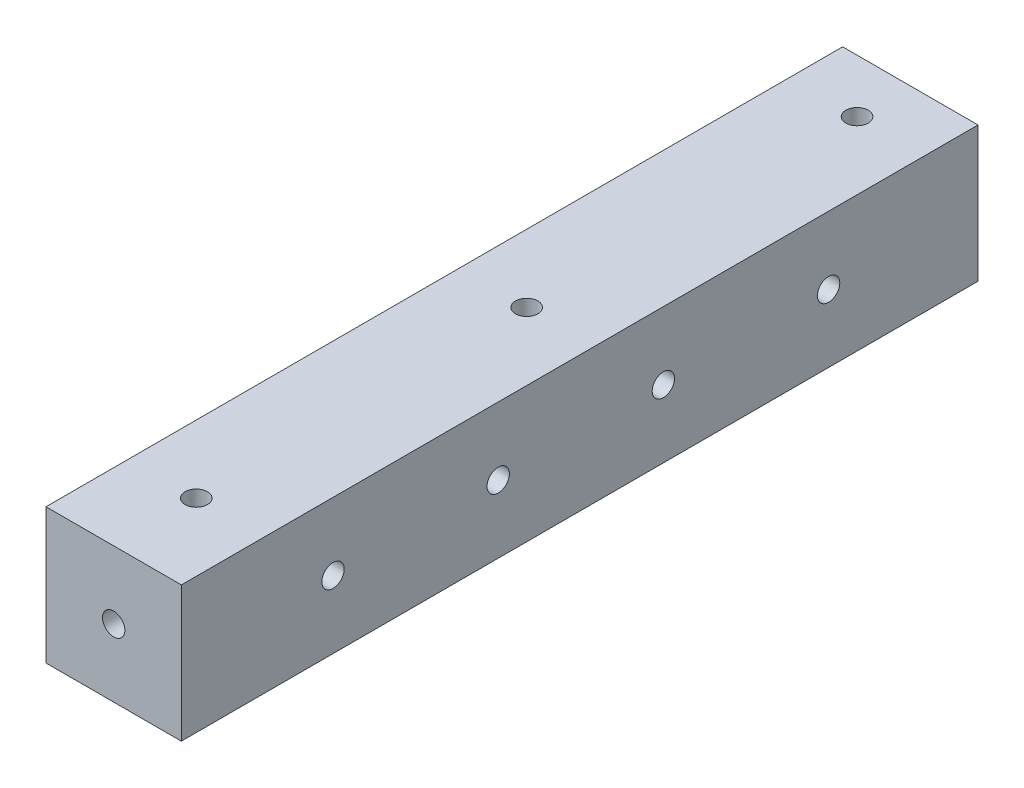
SolidWorks part; units mm, degrees
material "6061 Alloy"
ref_plane "Front Plane" through (0, 0, 0) normal (0, 0, 1) x (1, 0, 0)
ref_plane "Top Plane" through (0, 0, 0) normal (0, 1, 0) x (1, 0, 0)
ref_plane "Right Plane" through (0, 0, 0) normal (1, 0, 0) x (0, 0, -1)
sketch "Sketch1" plane through (0, 0, 0) normal (0, 0, 1) x (1, 0, 0)
  line L1 (-12.7, -12.7) -> (12.7, -12.7)
  line L2 (-12.7, -12.7) -> (-12.7, 12.7)
  line L3 (-12.7, 12.7) -> (12.7, 12.7)
  line L4 (12.7, -12.7) -> (12.7, 12.7)
  line L5 (-12.7, -12.7) -> (12.7, 12.7) construction
  line L6 (-12.7, 12.7) -> (12.7, -12.7) construction
  point P0 (0, 0)
  dimension "D1" = 25.4
extrude "Boss-Extrude1" add sketch "Sketch1" along normal mid plane 155
sketch "Sketch2" plane through (0, 0, 77.5) normal (0, 0, 1) x (1, 0, 0)
  point P0 (0, 0)
sketch "Sketch4" plane through (12.7, 0, 0) normal (1, 0, 0) x (0, 0, -1)
  line L0 (-77.5, -12.7) -> (-77.5, 12.7) construction
  point P0 (-46.5, 0)
  point P1 (-15.5, 0)
  point P2 (15.5, 0)
  point P3 (46.5, 0)
  dimension "D1" = 31
  dimension "D2" = 31
  dimension "D3" = 31
  dimension "D4" = 31
sketch "Sketch5" plane through (0, -12.7, 0) normal (0, -1, 0) x (1, 0, 0)
  line L0 (-12.7, 77.5) -> (12.7, 77.5) construction
  line L1 (-12.7, -77.5) -> (12.7, -77.5) construction
  point P0 (0, 62)
  point P1 (0, 0)
  point P2 (0, -62)
  dimension "D1" = 15.5
  dimension "D2" = 15.5
hole_wizard "M5x0.8 Tapped Hole3" positions "Sketch6" profile "Sketch8" tap size "M5x0.8" standard "ANSI Metric"
sketch "Sketch6" plane through (12.7, 0, 0) normal (1, 0, 0) x (0, 0, -1)
  point P0 (-46.5, 0)
  point P3 (-15.5, 0)
  point P6 (15.5, 0)
  point P9 (46.5, 0)
sketch "Sketch8" plane through (12.7, 0, 46.5) normal (0, 1, 0) x (0, 0, -1)
  line L0 (0, 0) -> (0, 25.4)
  line L1 (0, 25.4) -> (2.1, 25.4)
  line L2 (2.1, 25.4) -> (2.1, 0)
  line L5 (2.1, 0) -> (0, 0)
  line L11 (0, -6.35) -> (0, 107.95) construction
  dimension "Thru Tap Drill Dia." = 4.2
  dimension "Thru Tap Drill Depth" = 25.4
hole_wizard "M5x0.8 Tapped Hole2" positions "Sketch9" profile "Sketch10" tap size "M5x0.8" standard "ANSI Metric" end condition through all
sketch "Sketch9" plane through (0, -12.7, 0) normal (0, -1, 0) x (-1, 0, 0)
  point P0 (0, -62)
  point P3 (0, 0)
  point P6 (0, 62)
sketch "Sketch10" plane through (0, -12.7, 62) normal (1, 0, 0) x (0, 0, -1)
  line L0 (0, 0) -> (0, 25.4)
  line L1 (0, 25.4) -> (2.1, 25.4)
  line L2 (2.1, 25.4) -> (2.1, 0)
  line L5 (2.1, 0) -> (0, 0)
  line L11 (0, -6.35) -> (0, 107.95) construction
  dimension "Thru Tap Drill Dia." = 4.2
  dimension "Thru Tap Drill Depth" = 25.4
hole_wizard "M5x0.8 Tapped Hole1" positions "Sketch11" profile "Sketch12" tap size "M5x0.8" standard "ANSI Metric"
sketch "Sketch11" plane through (0, 0, 77.5) normal (0, 0, 1) x (1, 0, 0)
  point P0 (0, 0)
sketch "Sketch12" plane through (0, 0, 77.5) normal (1, 0, 0) x (0, -1, 0)
  line L0 (0, 0) -> (0, 11.2618)
  line L1 (0, 11.2618) -> (2.1, 10)
  line L2 (2.1, 10) -> (2.1, 0)
  line L5 (2.1, 0) -> (0, 0)
  line L10 (0, 11.2618) -> (-2.1, 10) construction
  line L11 (0, -6.35) -> (0, 107.95) construction
  dimension "Tap Drill Dia." = 4.2
  dimension "Tap Drill Depth" = 10
  dimension "Drill Angle" = 118
sketch "Sketch13" plane through (0, 12.7, 0) normal (0, 1, 0) x (1, 0, 0)
  line L0 (12.7, -77.5) -> (12.7, 77.5) construction
  line L1 (12.7, 72) -> (-12.7, 72)
  line L2 (12.7, 72) -> (12.7, 77.5)
  line L3 (12.7, 77.5) -> (-12.7, 77.5)
  line L4 (-12.7, 72) -> (-12.7, 77.5)
  line L5 (-12.7, -77.5) -> (-12.7, 77.5) construction
  line L6 (12.7, 77.5) -> (-12.7, 77.5) construction
  circle A0 centre (0, 62) radius 2.1 construction
  dimension "D1" = 10
extrude "Cut-Extrude1" cut sketch "Sketch13" against normal through all
hole_wizard "Tap Drill for M5x0.8 Tap1" positions "Sketch14" profile "Sketch15" hole size "M5x0.8" standard "ANSI Metric" end condition through all
sketch "Sketch14" plane through (12.7, 0, 0) normal (1, 0, 0) x (0, 0, -1)
  line L7 (-77.5, -12.7) -> (-77.5, 12.7) construction
  point P0 (-49.04, 0)
  point P2 (-18.04, 0)
  point P4 (12.96, 0)
  point P6 (43.96, 0)
  point P31 (0, 0)
  dimension "D2" = 28.46
sketch "Sketch15" plane through (12.7, 0, 49.04) normal (0, 1, 0) x (0, 0, -1)
  line L0 (0, 0) -> (0, 25.4)
  line L1 (0, 25.4) -> (2.1, 25.4)
  line L2 (2.1, 25.4) -> (2.1, 0)
  line L5 (2.1, 0) -> (0, 0)
  line L11 (0, -6.35) -> (0, 107.95) construction
  dimension "Thru Hole Dia." = 4.2
  dimension "Thru Hole Depth" = 25.4
